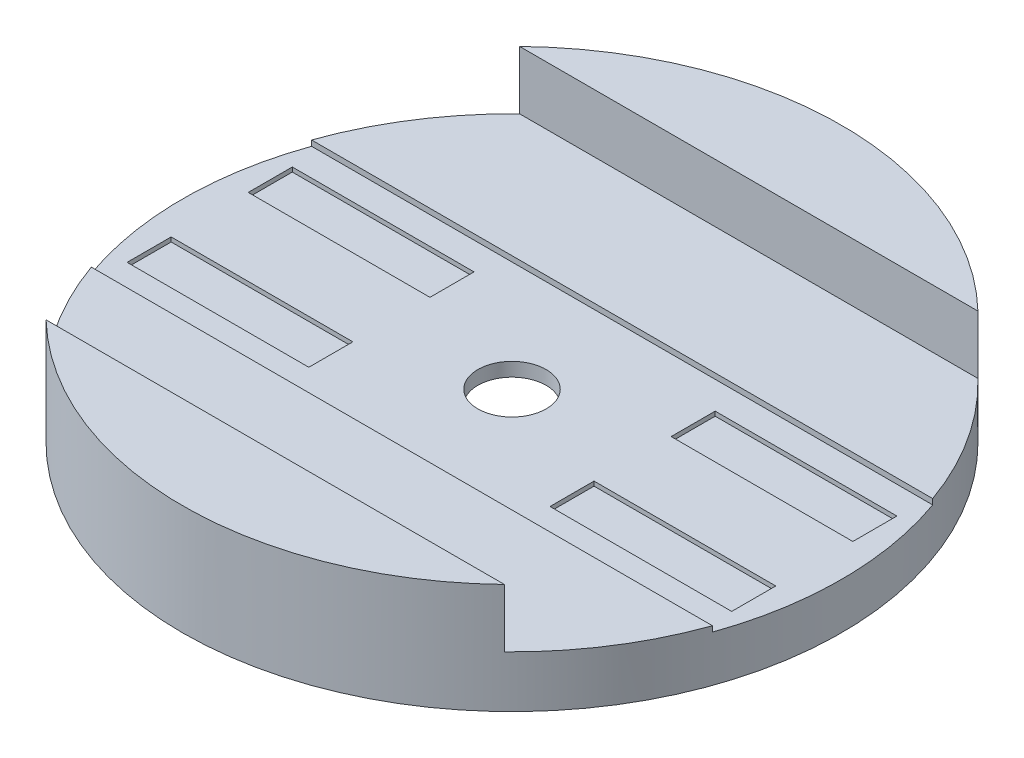
SolidWorks part; units mm, degrees
ref_plane "Front Plane" through (0, 0, 0) normal (0, 0, 1) x (1, 0, 0)
ref_plane "Top Plane" through (0, 0, 0) normal (0, 1, 0) x (1, 0, 0)
ref_plane "Right Plane" through (0, 0, 0) normal (1, 0, 0) x (0, 0, -1)
sketch "Sketch1" plane through (0, 0, 0) normal (0, 1, 0) x (1, 0, 0)
  circle A0 centre (0, 0) radius 76
  dimension "D1" = 152
extrude "Boss-Extrude1" add sketch "Sketch1" along normal blind 25.4 contours A0
sketch "Sketch2" plane through (0, 25.4, 0) normal (0, 1, 0) x (1, 0, 0)
  line L0 (-76, 0) -> (76, 0) construction
  line L1 (-58.008, 0) -> (58.008, 0) construction
  line L2 (-58.008, 54.61) -> (58.008, 54.61)
  line L3 (-58.008, -54.61) -> (58.008, -54.61)
  circle A0 centre (0, 0) radius 76 construction
  arc A1 (-58.008, 54.61) -> (-58.008, -54.61) centre (-58.008, 0) ccw
  arc A2 (58.008, -54.61) -> (58.008, 54.61) centre (58.008, 0) ccw
  point P7 (0, 0)
  dimension "D1" = 54.61
extrude "Cut-Extrude4" cut sketch "Sketch2" against normal blind 13.462
sketch "Sketch5" plane through (0, 11.938, 0) normal (0, 1, 0) x (1, 0, 0)
  line L0 (0, 7.874) -> (0, -7.874)
  circle A0 centre (0, 0) radius 7.874
  dimension "D1" = 15.748
extrude "Cut-Extrude5" cut sketch "Sketch5" against normal blind 20 contours A0
sketch "Sketch7" plane through (0, 11.938, 0) normal (0, 1, 0) x (1, 0, 0)
  line L0 (-50.1251, 42.3228) -> (-67.9029, 6.4906)
  line L1 (-67.9029, 6.4906) -> (-22.9029, 6.4906)
  line L2 (-22.9029, 6.4906) -> (-50.1251, 42.3228)
  line L3 (0, 54.61) -> (0, -54.61) construction
  line L4 (52.8559, 54.61) -> (-52.8559, 54.61) construction
  line L5 (-52.8559, -54.61) -> (52.8559, -54.61) construction
  line L6 (67.9029, 6.4906) -> (22.9029, 6.4906)
  line L7 (50.1251, 42.3228) -> (67.9029, 6.4906)
  line L8 (22.9029, 6.4906) -> (50.1251, 42.3228)
  line L9 (-76, 0) -> (76, 0) construction
  line L10 (50.1251, -42.3228) -> (67.9029, -6.4906)
  line L11 (22.9029, -6.4906) -> (50.1251, -42.3228)
  line L12 (67.9029, -6.4906) -> (22.9029, -6.4906)
  line L13 (-67.9029, -6.4906) -> (-22.9029, -6.4906)
  line L14 (-50.1251, -42.3228) -> (-67.9029, -6.4906)
  line L15 (-22.9029, -6.4906) -> (-50.1251, -42.3228)
  arc A0 (-52.8559, 54.61) -> (-52.8559, -54.61) centre (0, 0) ccw construction
  arc A1 (52.8559, -54.61) -> (52.8559, 54.61) centre (0, 0) ccw construction
  dimension "D1" = 40
  dimension "D2" = 45
  dimension "D3" = 45
extrude "Cut-Extrude6" [suppressed] cut sketch "Sketch7" against normal through all
sketch "Sketch9" [suppressed] plane through (0, 11.938, 0) normal (0, 1, 0) x (1, 0, 0)
  line L0 (-12.5, 6.4906) -> (-12.5, 42.3228)
  line L1 (-12.5, 42.3228) -> (-39.5, 42.3228)
  line L2 (-12.5, 6.4906) -> (-39.5, 42.3228)
  line L3 (0, 54.61) -> (0, -54.61) construction
  line L4 (52.8559, 54.61) -> (-52.8559, 54.61) construction
  line L5 (-52.8559, -54.61) -> (52.8559, -54.61) construction
  line L6 (-76, 0) -> (76, 0) construction
  line L7 (12.5, 6.4906) -> (39.5, 42.3228)
  line L8 (12.5, 42.3228) -> (39.5, 42.3228)
  line L9 (12.5, 6.4906) -> (12.5, 42.3228)
  line L10 (12.5, -6.4906) -> (12.5, -42.3228)
  line L11 (12.5, -42.3228) -> (39.5, -42.3228)
  line L12 (12.5, -6.4906) -> (39.5, -42.3228)
  line L13 (-12.5, -6.4906) -> (-39.5, -42.3228)
  line L14 (-12.5, -42.3228) -> (-39.5, -42.3228)
  line L15 (-12.5, -6.4906) -> (-12.5, -42.3228)
  arc A0 (-52.8559, 54.61) -> (-52.8559, -54.61) centre (0, 0) ccw construction
  arc A1 (52.8559, -54.61) -> (52.8559, 54.61) centre (0, 0) ccw construction
  dimension "D1" = 27
  dimension "D2" = 12.5
  dimension "D3" = 27
extrude "Cut-Extrude7" [suppressed] cut sketch "Sketch9" against normal through all
sketch "Sketch10" [suppressed] plane through (0, 11.938, 0) normal (0, 1, 0) x (1, 0, 0)
  line L0 (-22.9029, 6.4906) -> (-50.1251, 42.3228) construction
  line L1 (-39.5, 42.3228) -> (-12.5, 6.4906) construction
  dimension "D1" = 16.5359
sketch "Sketch11" plane through (0, 0, 0) normal (0, -1, 0) x (1, 0, 0)
sketch "Sketch13" plane through (0, 0, 0) normal (0, -1, 0) x (-1, 0, 0)
  circle A0 centre (0, 0) radius 70
  dimension "D1" = 140
extrude "Cut-Extrude9" cut sketch "Sketch13" against normal blind 7.5
sketch "Sketch15" plane through (0, 11.938, 0) normal (0, 1, 0) x (1, 0, 0)
  line L0 (76, 0) -> (-76, 0) construction
  line L1 (76, -25.4) -> (-76, -25.4)
  line L2 (76, 25.4) -> (-76, 25.4)
  arc A0 (-52.8559, 54.61) -> (-52.8559, -54.61) centre (0, 0) ccw construction
  arc A1 (76, -25.4) -> (76, 25.4) centre (76, 0) ccw
  arc A2 (-76, 25.4) -> (-76, -25.4) centre (-76, 0) ccw
  point P6 (0, 0)
  dimension "D1" = 25.4
extrude "Cut-Extrude11" cut sketch "Sketch15" against normal blind 1.27
sketch "Sketch16" plane through (0, 10.668, 0) normal (0, 1, 0) x (1, 0, 0)
  line L1 (71.6299, 25.4) -> (-71.6299, 25.4) construction
  line L4 (-69.723, -8.89) -> (-27.813, -8.89)
  line L5 (-69.723, 19.05) -> (-27.813, 19.05)
  line L6 (-69.723, 19.05) -> (-69.723, 8.89)
  line L7 (-69.723, 8.89) -> (-27.813, 8.89)
  line L8 (-27.813, 19.05) -> (-27.813, 8.89)
  line L9 (-27.813, -19.05) -> (-27.813, -8.89)
  line L10 (-69.723, -19.05) -> (-27.813, -19.05)
  line L11 (-69.723, -19.05) -> (-69.723, -8.89)
  line L12 (69.723, -19.05) -> (69.723, -8.89)
  line L13 (69.723, -19.05) -> (27.813, -19.05)
  line L14 (27.813, -19.05) -> (27.813, -8.89)
  line L15 (69.723, -8.89) -> (27.813, -8.89)
  line L16 (69.723, 8.89) -> (27.813, 8.89)
  line L17 (27.813, 19.05) -> (27.813, 8.89)
  line L18 (69.723, 19.05) -> (27.813, 19.05)
  line L19 (69.723, 19.05) -> (69.723, 8.89)
  dimension "D1" = 6.35
  dimension "D2" = 41.91
  dimension "D3" = 10.16
  dimension "D4" = 55.626
extrude "Cut-Extrude12" cut sketch "Sketch16" against normal blind 1.016
